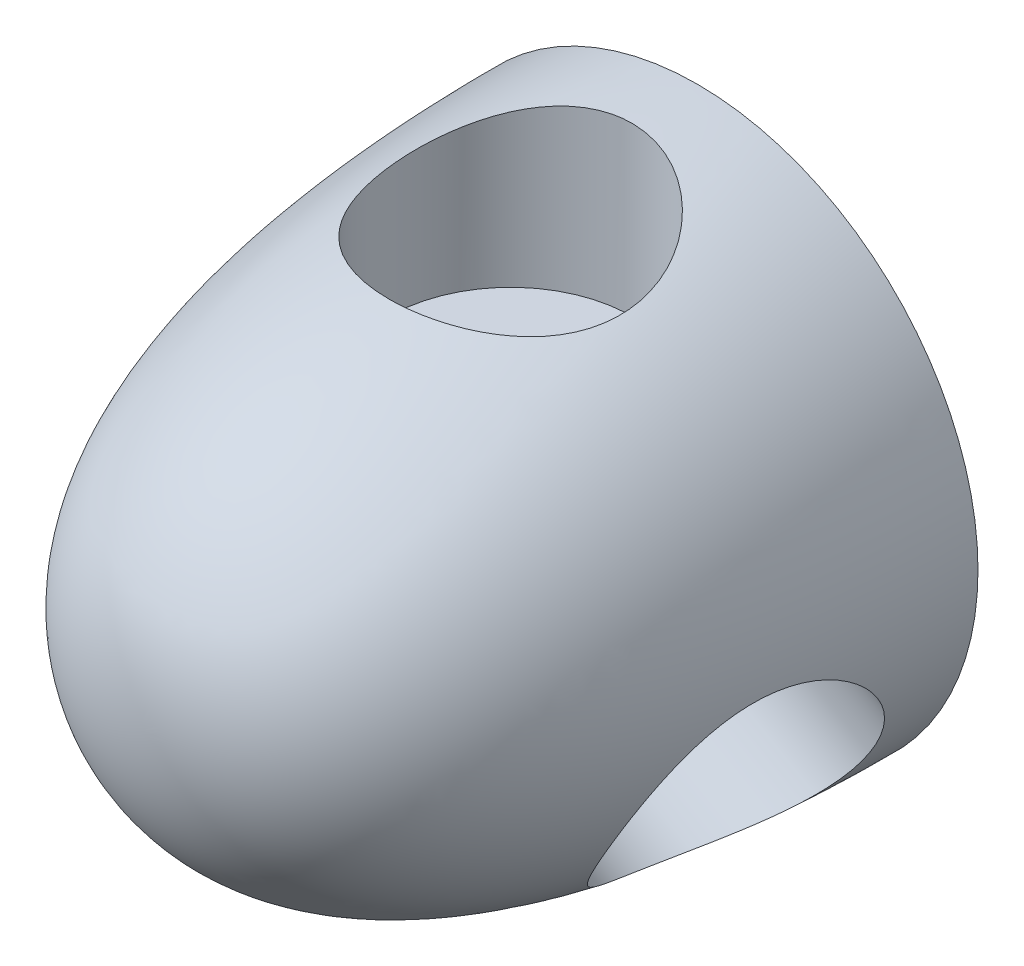
SolidWorks part; units mm, degrees
ref_plane "Front Plane" through (0, 0, 0) normal (0, 0, 1) x (1, 0, 0)
ref_plane "Top Plane" through (0, 0, 0) normal (0, 1, 0) x (1, 0, 0)
ref_plane "Right Plane" through (0, 0, 0) normal (1, 0, 0) x (0, 0, -1)
sketch "Sketch1" plane through (0, 0, 0) normal (1, 0, 0) x (0, 0, -1)
  line L0 (-26.4035, 0) -> (26.4035, 0) construction
  line L1 (0, 0) -> (38.1, 0)
  line L2 (38.1, 0) -> (38.1, 19.05)
  line L3 (0, 0) -> (0, 19.05) construction
  line L4 (0, 19.05) -> (38.1, 19.05) construction
  spline S0 degree 3 poles (0, 0) (0, 16.9337) (23.901, 19.05) (38.1, 19.05) knots 0 0 0 0 1 1 1 1
  dimension "D1" = 38.1
  dimension "D2" = 38.1
revolve "Revolve1" add sketch "Sketch1" angle 360 about L0
sketch "Sketch2" plane through (0, 0, -38.1) normal (0, 0, -1) x (-1, 0, 0)
  circle A0 centre (0, 0) radius 4.826
  dimension "D1" = 9.652
extrude "Cut-Extrude1" cut sketch "Sketch2" against normal blind 12.7
sketch "Sketch4" plane through (0, 0, 0) normal (1, 0, 0) x (0, 0, -1)
  line L0 (-8.2204, 0) -> (44.5117, 0) construction
ref_plane "Plane1" through (0, 7.62, 0) normal (0, 1, 0) x (1, 0, 0)
sketch "Sketch5" plane through (0, 7.62, 0) normal (0, 1, 0) x (1, 0, 0)
  line L0 (0, -8.2204) -> (0, 44.5117) construction
  line L1 (4.826, 38.1) -> (-4.826, 38.1) construction
  circle A0 centre (0, 25.4) radius 8.255
  dimension "D2" = 16.51
  dimension "D1" = 12.7
extrude "Cut-Extrude2" cut sketch "Sketch5" along normal up to surface (9.2645 mm away)
pattern_circular "CirPattern1" count 3 over 360 about axis through (0, 0, 0) along (0, 0, 1) of "Cut-Extrude2"
